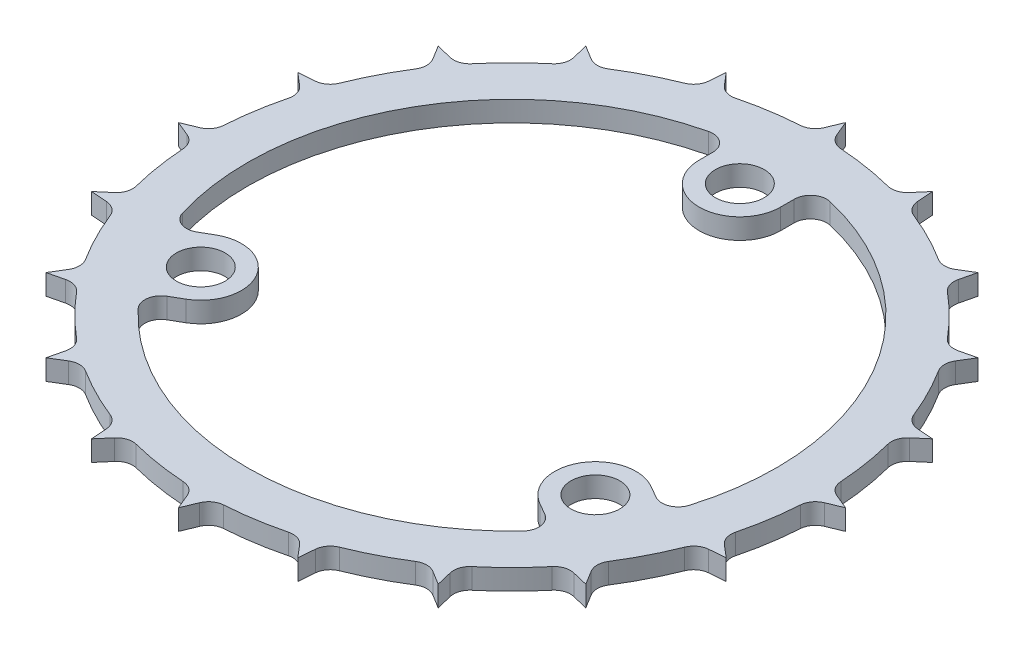
SolidWorks part; units mm, degrees
material "Titanium Ti-8Al-1Mo-1V"
ref_plane "Front Plane" through (0, 0, 0) normal (0, 0, 1) x (1, 0, 0)
ref_plane "Top Plane" through (0, 0, 0) normal (0, 1, 0) x (1, 0, 0)
ref_plane "Right Plane" through (0, 0, 0) normal (1, 0, 0) x (0, 0, -1)
other "Bounding Box"
ref_plane "Default Plane" through (13.8565, 3.175, 6.7999) normal (0, -1, 0) x (-1, 0, 0)
sketch "Sketch1" plane through (0, 0, 0) normal (0, 1, 0) x (1, 0, 0)
  circle A0 centre (0, 0) radius 24.13
  dimension "D1" = 48.26
extrude "Boss-Extrude1" add sketch "Sketch1" along normal mid plane 1.6002
sketch "Sketch2" plane through (0, 0.8001, 0) normal (0, 1, 0) x (1, 0, 0)
  line L0 (-0.7945, 24.1169) -> (0, 26.035)
  line L1 (0, 26.035) -> (0.7945, 24.1169)
  line L2 (0, 26.035) -> (0, 0) construction
  line L3 (-0.7945, 24.1169) -> (0.7945, 24.1169)
  circle A0 centre (0, 0) radius 24.13 construction
  dimension "D1" = 26.035
  dimension "D2" = 45
extrude "Boss-Extrude2" add sketch "Sketch2" against normal through all
fillet "Fillet1" radius 1.27 2 edges at (0.7945, 0, -24.1169) (-0.7945, 0, -24.1169)
pattern_circular "CirPattern1" count 20 over 360 about axis through (0, 0, 0) along (0, 1, 0) of "Fillet1", "Boss-Extrude2"
sketch "Sketch3" plane through (0, 0.8001, 0) normal (0, 1, 0) x (1, 0, 0)
  circle A0 centre (0, 0) radius 20.6375
  dimension "D1" = 41.275
extrude "Cut-Extrude1" cut sketch "Sketch3" against normal through all
sketch "Sketch4" plane through (0, 0.8001, 0) normal (0, 1, 0) x (1, 0, 0)
  line L0 (-3.175, 17.78) -> (-3.175, 20.3918)
  line L1 (3.175, 17.78) -> (3.175, 20.3918)
  line L2 (0, 0) -> (0, 17.78) construction
  circle A0 centre (0, 17.78) radius 1.905
  arc A1 (-3.175, 17.78) -> (3.175, 17.78) centre (0, 17.78) ccw
  circle A2 centre (0, 0) radius 20.6375 construction
  arc A3 (-3.175, 20.3918) -> (3.175, 20.3918) centre (0, 0) cw
  arc A4 (3.175, 17.78) -> (-3.175, 17.78) centre (0, 17.78) ccw construction
  dimension "D1" = 3.81
  dimension "D2" = 6.35
  dimension "D3" = 17.78
extrude "Boss-Extrude3" add sketch "Sketch4" against normal through all
fillet "Fillet2" radius 1.27 2 edges at (3.175, 0, -20.3918) (-3.175, 0, -20.3918)
pattern_circular "CirPattern2" count 3 over 360 about axis through (0, 0, 0) along (0, 1, 0) of "Fillet2", "Boss-Extrude3"
